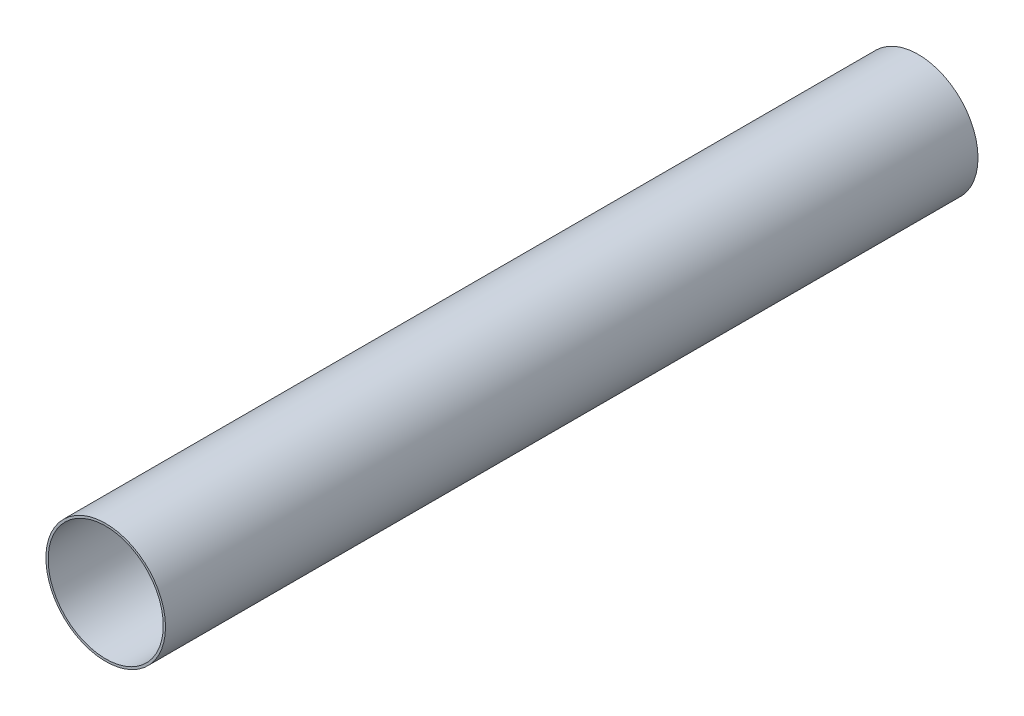
SolidWorks part; units mm, degrees
ref_plane "Front Plane" through (0, 0, 0) normal (0, 0, 1) x (1, 0, 0)
ref_plane "Top Plane" through (0, 0, 0) normal (0, 1, 0) x (1, 0, 0)
ref_plane "Right Plane" through (0, 0, 0) normal (1, 0, 0) x (0, 0, -1)
sketch "Sketch1" plane through (0, 0, 0) normal (0, 0, 1) x (1, 0, 0)
  circle A0 centre (0, 0) radius 64.77
  circle A1 centre (0, 0) radius 67.31
  dimension "D1" = 2.54
  dimension "D2" = 129.54
extrude "Boss-Extrude1" add sketch "Sketch1" along normal blind 914.4
